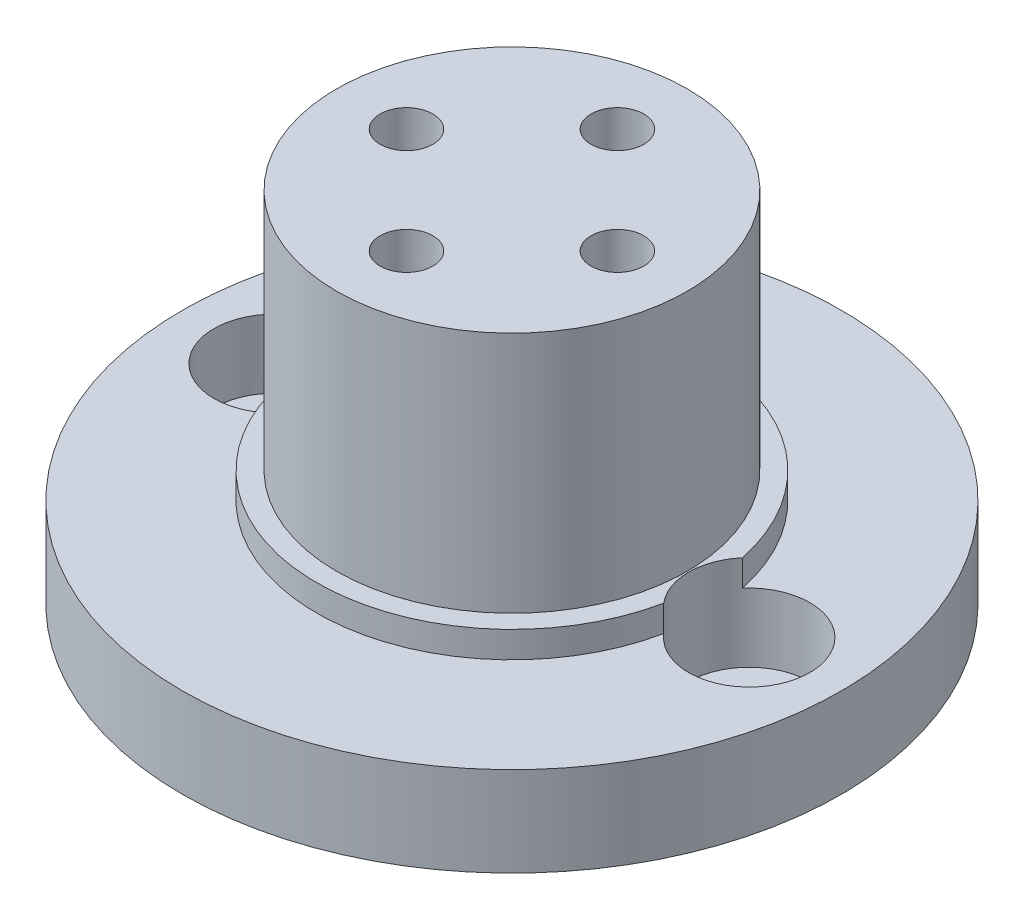
SolidWorks part; units mm, degrees
ref_plane "Front Plane" through (0, 0, 0) normal (0, 0, 1) x (1, 0, 0)
ref_plane "Top Plane" through (0, 0, 0) normal (0, 1, 0) x (1, 0, 0)
ref_plane "Right Plane" through (0, 0, 0) normal (1, 0, 0) x (0, 0, -1)
sketch "Sketch1" plane through (0, 0, 0) normal (0, 1, 0) x (1, 0, 0)
  circle A0 centre (0, 0) radius 15.875
  dimension "D1" = 31.75
extrude "Boss-Extrude1" add sketch "Sketch1" along normal blind 4.318
sketch "Sketch4" plane through (0, 4.318, 0) normal (0, 1, 0) x (1, 0, 0)
  circle A0 centre (0, 0) radius 9.398
  dimension "D1" = 18.796
extrude "Boss-Extrude2" add sketch "Sketch4" along normal blind 12.954
sketch "Sketch5" plane through (0, 4.318, 0) normal (0, 1, 0) x (1, 0, 0)
  circle A0 centre (-11.43, 0) radius 2.921
  circle A1 centre (11.43, 0) radius 2.921
  dimension "D1" = 5.842
  dimension "D2" = 5.842
  dimension "D3" = 22.86
  dimension "D4" = 11.43
extrude "Cut-Extrude1" cut sketch "Sketch5" against normal blind 3.302 and the other way through all
sketch "Sketch6" plane through (0, 4.318, 0) normal (0, 1, 0) x (1, 0, 0)
  circle A0 centre (-11.43, 0) radius 1.4605
  circle A1 centre (11.43, 0) radius 1.7371
  dimension "D1" = 2.921
extrude "Cut-Extrude2" cut sketch "Sketch6" against normal through all both
sketch "Sketch10" plane through (0, 17.272, 0) normal (0, 1, 0) x (1, 0, 0)
  circle A0 centre (0, 5.08) radius 1.27
  circle A1 centre (0, -5.08) radius 1.27
  circle A2 centre (5.08, 0) radius 1.27
  circle A3 centre (-5.08, 0) radius 1.27
  dimension "D1" = 2.54
  dimension "D2" = 2.54
  dimension "D5" = 2.54
  dimension "D6" = 2.54
  dimension "D3" = 5.08
  dimension "D4" = 10.16
  dimension "D7" = 10.16
  dimension "D8" = 5.08
extrude "Cut-Extrude6" cut sketch "Sketch10" against normal through all
sketch "Sketch12" plane through (0, 17.272, 0) normal (0, 1, 0) x (1, 0, 0)
  circle A0 centre (0, 0) radius 8.4455
  circle A1 centre (0, 0) radius 9.398
  dimension "D1" = 16.891
extrude "Cut-Extrude8" cut sketch "Sketch12" against normal blind 11.684
sketch "Sketch13" plane through (0, 0, 0) normal (0, -1, 0) x (1, 0, 0)
  line L7 (7.4264, 0) -> (6.2532, 2.032)
  line L8 (6.2532, 2.032) -> (3.9068, 2.032)
  line L9 (3.9068, 2.032) -> (2.7336, 0)
  line L10 (2.7336, 0) -> (3.9068, -2.032)
  line L11 (3.9068, -2.032) -> (6.2532, -2.032)
  line L12 (6.2532, -2.032) -> (7.4264, 0)
  line L13 (2.3464, -5.08) -> (1.1732, -3.048)
  line L14 (1.1732, -3.048) -> (-1.1732, -3.048)
  line L15 (-1.1732, -3.048) -> (-2.3464, -5.08)
  line L16 (-2.3464, -5.08) -> (-1.1732, -7.112)
  line L17 (-1.1732, -7.112) -> (1.1732, -7.112)
  line L18 (1.1732, -7.112) -> (2.3464, -5.08)
  line L19 (-2.7336, 0) -> (-3.9068, 2.032)
  line L20 (-3.9068, 2.032) -> (-6.2532, 2.032)
  line L21 (-6.2532, 2.032) -> (-7.4264, 0)
  line L22 (-7.4264, 0) -> (-6.2532, -2.032)
  line L23 (-6.2532, -2.032) -> (-3.9068, -2.032)
  line L24 (-3.9068, -2.032) -> (-2.7336, 0)
  line L25 (2.3464, 5.08) -> (1.1732, 7.112)
  line L26 (1.1732, 7.112) -> (-1.1732, 7.112)
  line L27 (-1.1732, 7.112) -> (-2.3464, 5.08)
  line L28 (-2.3464, 5.08) -> (-1.1732, 3.048)
  line L29 (-1.1732, 3.048) -> (1.1732, 3.048)
  line L30 (1.1732, 3.048) -> (2.3464, 5.08)
  circle A0 centre (0, 5.08) radius 2.032 construction
  circle A1 centre (5.08, 0) radius 2.032 construction
  circle A2 centre (0, -5.08) radius 2.032 construction
  circle A3 centre (-5.08, 0) radius 2.032 construction
  dimension "D1" = 4.064
  dimension "D2" = 4.064
  dimension "D3" = 4.064
  dimension "D4" = 4.064
extrude "Cut-Extrude9" cut sketch "Sketch13" against normal blind 10.16
